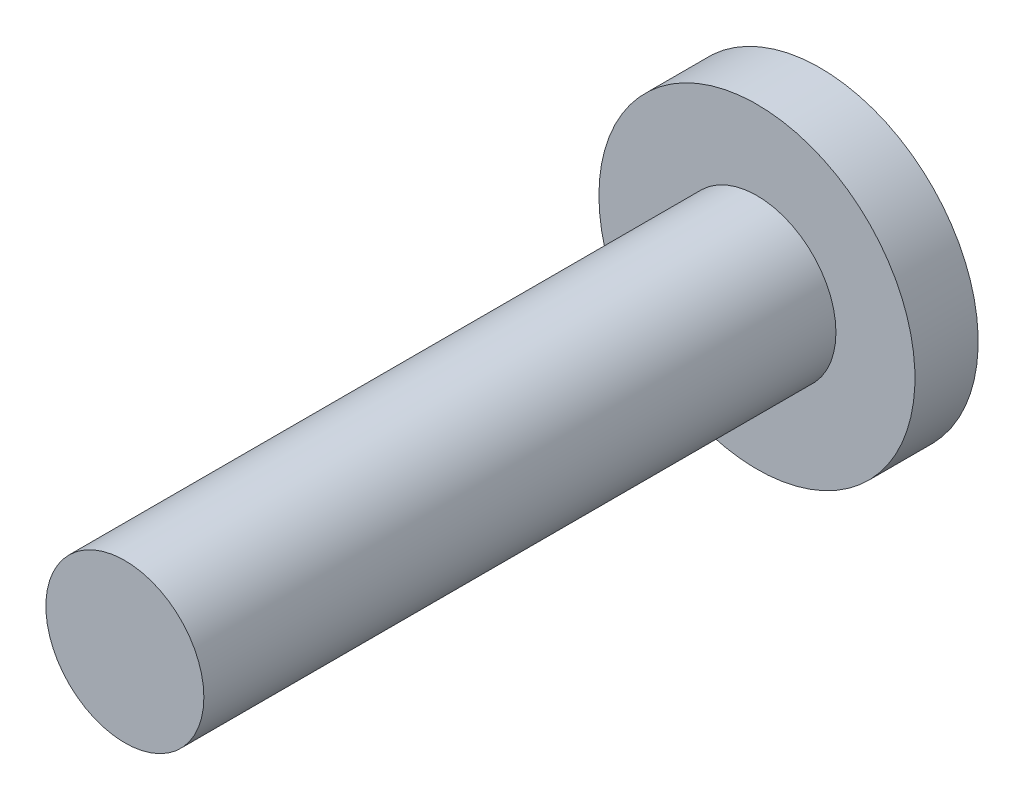
SolidWorks part; units mm, degrees
material "Stainless Steel (ferritic)"
ref_plane "Front Plane" through (0, 0, 0) normal (0, 0, 1) x (1, 0, 0)
ref_plane "Top Plane" through (0, 0, 0) normal (0, 1, 0) x (1, 0, 0)
ref_plane "Right Plane" through (0, 0, 0) normal (1, 0, 0) x (0, 0, -1)
sketch "Sketch1" plane through (0, 0, 0) normal (0, 0, 1) x (1, 0, 0)
  circle A0 centre (0, 0) radius 3.175
  dimension "D1" = 6.35
extrude "Boss-Extrude1" add sketch "Sketch1" along normal blind 25.4
sketch "Sketch2" plane through (0, 0, 0) normal (0, 0, -1) x (-1, 0, 0)
  circle A0 centre (0, 0) radius 6.35
  dimension "D1" = 12.7
extrude "Boss-Extrude2" add sketch "Sketch2" along normal blind 2.54
